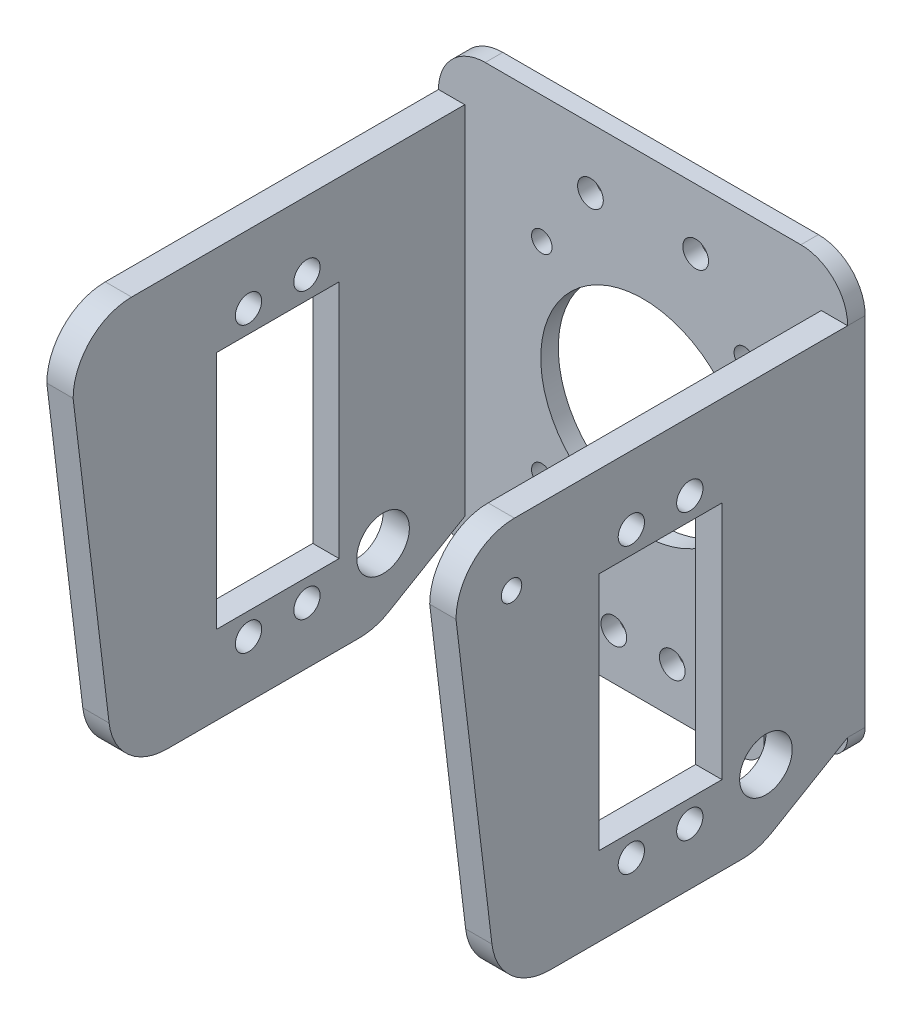
SolidWorks part; units mm, degrees
ref_plane "前视基准面" through (0, 0, 0) normal (0, 0, 1) x (1, 0, 0)
ref_plane "上视基准面" through (0, 0, 0) normal (0, 1, 0) x (1, 0, 0)
ref_plane "右视基准面" through (0, 0, 0) normal (1, 0, 0) x (0, 0, -1)
sketch "草图2" plane through (0, 0, 0) normal (0, 0, 1) x (1, 0, 0)
  line L0 (-31, -34) -> (-20.7251, -34)
  line L1 (-16.7251, -42) -> (16.7251, -42)
  line L2 (-35, -30) -> (-35, 31)
  line L3 (-27, 39) -> (27, 39)
  line L4 (35, -30) -> (35, 31)
  line L5 (-37.7907, -42.1097) -> (35, 39) construction
  line L6 (-35, 39) -> (30.3247, -33.7903) construction
  line L7 (-20.7251, -34) -> (-20.7251, -38)
  line L8 (0, 44.0576) -> (0, -51.8326) construction
  line L9 (20.7251, -34) -> (20.7251, -38)
  line L10 (31, -34) -> (20.7251, -34)
  line L16 (-17.3241, -17.3241) -> (17.3241, -17.3241) construction
  line L17 (-17.3241, -17.3241) -> (-17.3241, 17.3241) construction
  line L18 (-17.3241, 17.3241) -> (17.3241, 17.3241) construction
  line L19 (17.3241, -17.3241) -> (17.3241, 17.3241) construction
  line L20 (-17.3241, -17.3241) -> (17.3241, 17.3241) construction
  line L21 (-17.3241, 17.3241) -> (17.3241, -17.3241) construction
  arc A1 (-27, 39) -> (-35, 31) centre (-27, 31) ccw
  arc A2 (35, 31) -> (27, 39) centre (27, 31) ccw
  arc A3 (-31, -34) -> (-35, -30) centre (-31, -30) cw
  arc A4 (-16.7251, -42) -> (-20.7251, -38) centre (-16.7251, -38) cw
  arc A5 (20.7251, -38) -> (16.7251, -42) centre (16.7251, -38) cw
  arc A6 (35, -30) -> (31, -34) centre (31, -30) cw
  circle A19 centre (0, 0) radius 17.5
  circle A21 centre (-17.3241, 17.3241) radius 1.75
  circle A22 centre (17.3241, 17.3241) radius 1.75
  circle A23 centre (17.3241, -17.3241) radius 1.75
  circle A24 centre (-17.3241, -17.3241) radius 1.75
  point P0 (0, 0)
  point P24 (-35, -34)
  point P27 (-20.7251, -42)
  point P30 (20.7251, -42)
  point P33 (35, -34)
  point P45 (0, 0)
  point P49 (0, 0)
  point P50 (0, 0)
  dimension "D3" = 35
  dimension "D4" = 8
  dimension "D5" = 8
  dimension "D6" = 4
  dimension "D7" = 4
  dimension "D8" = 4
  dimension "D9" = 4
  dimension "D10" = 90
  dimension "D12" = 3.5
  dimension "D2" = 81
  dimension "D11" = 24.5
  dimension "D13" = 35
  dimension "D14" = 39
  dimension "D15" = 73
  dimension "D16" = 4
extrude "凸台-拉伸2" add sketch "草图2" along normal blind 3
sketch "草图4" plane through (0, 0, 3) normal (0, 0, 1) x (1, 0, 0)
  line L0 (35, -30) -> (35, 31) construction
  line L1 (30.5, -39) -> (35, -39)
  line L2 (30.5, -39) -> (30.5, 31)
  line L3 (30.5, 31) -> (35, 31)
  line L4 (35, -39) -> (35, 31)
  dimension "D1" = 4.5
  dimension "D2" = 70
extrude "凸台-拉伸3" add sketch "草图4" along normal blind 67 contours L2 L1 L4 L3
sketch "草图5" plane through (35, 0, 0) normal (1, 0, 0) x (0, 0, -1)
  line L2 (-3, -30) -> (0, -30) construction
  line L3 (-3, -39) -> (-3, -30) construction
  line L4 (-70, -39) -> (-3, -39) construction
  line L5 (-70, 31) -> (-3, 31) construction
  line L8 (-3, -30) -> (0, -30)
  line L9 (-3, -39) -> (-3, -30)
  line L10 (-53.9224, -39) -> (-21.0514, -39)
  line L11 (-60, 31) -> (-3, 31)
  line L12 (-3, 31) -> (-3, -30)
  line L13 (-70, 21) -> (-63.8511, -30.1926)
  line L15 (-28.4612, -39) -> (-53.9224, -39)
  line L17 (-15.9894, -37.6242) -> (-3, -30)
  line L19 (-21.0514, -39) -> (-3, -39)
  line L20 (-3, -30) -> (-3, -39)
  line L21 (-70, 21) -> (-70, 31)
  line L22 (-60, 31) -> (-70, 31)
  line L26 (0, -30) -> (0, 31)
  line L27 (0, 31) -> (-3, 31)
  line L28 (-3, 31) -> (-70, 31)
  line L29 (-70, 31) -> (-70, -39)
  line L30 (-70, -39) -> (-3, -39)
  line L31 (-3, -39) -> (-3, -30)
  line L32 (-3, -30) -> (0, -30)
  line L33 (0, -30) -> (0, 31)
  line L34 (0, 31) -> (-3, 31)
  line L35 (-3, 31) -> (-70, 31)
  line L36 (-70, 31) -> (-70, -39)
  line L37 (-70, -39) -> (-3, -39)
  line L38 (-3, -39) -> (-3, -30)
  line L39 (-3, -30) -> (0, -30)
  arc A0 (-70, 21) -> (-60, 31) centre (-60, 21) cw
  arc A1 (-53.9224, -39) -> (-63.8511, -30.1926) centre (-53.9224, -29) cw
  arc A2 (-15.9894, -37.6242) -> (-21.0514, -39) centre (-21.0514, -29) cw
  point P17 (-21.0514, -39)
  point P18 (-3, -30)
  line M12 (-3, 31) -> (-70, 31)
  line M13 (-70, 31) -> (-70, -39)
  line M14 (-70, -39) -> (-3, -39)
  line M15 (-3, -39) -> (-3, -30)
  dimension "D1" = 10
  dimension "D2" = 10
  dimension "D3" = 10
  dimension "D4" = 0
extrude "切除-拉伸4" cut sketch "草图5" against normal through all contours A0 M13 M12 | A1 L13 M14 M13 | L17 A2 M14 M15
mirror "镜向2" about plane through (0, 0, 0) normal (1, 0, 0) of "切除-拉伸4", "凸台-拉伸3"
sketch "草图6" plane through (35, 0, 0) normal (1, 0, 0) x (0, 0, -1)
  line L0 (0, 38.5) -> (0, -38.5) construction
  line L5 (-45.5, -32) -> (-24.5, -32)
  line L6 (-45.5, -32) -> (-45.5, 22)
  line L7 (-45.5, 22) -> (-24.5, 22)
  line L8 (-35, 22) -> (-35, -32) construction
  line L9 (-45.5, -5) -> (-24.5, -5) construction
  line L10 (-24.5, -32) -> (-24.5, 22)
  line L11 (-45.5, -32) -> (-24.5, 22) construction
  line L12 (-45.5, 22) -> (-24.5, -32) construction
  line L13 (-53.9224, -39) -> (-21.0514, -39) construction
  line L15 (-45.5, -25.5) -> (-24.5, -25.5)
  line L16 (-45.5, -25.5) -> (-45.5, 15.5)
  line L17 (-45.5, 15.5) -> (-24.5, 15.5)
  line L18 (-24.5, -25.5) -> (-24.5, 15.5)
  line L19 (-45.5, -25.5) -> (-24.5, 15.5) construction
  line L20 (-45.5, 15.5) -> (-24.5, -25.5) construction
  circle A0 centre (-40, -29.315) radius 2.25
  circle A2 centre (-30, -29.315) radius 2.25
  circle A3 centre (-30, 19.315) radius 2.25
  circle A4 centre (-40, 19.315) radius 2.25
  point P0 (-35, -5)
  point P21 (-35, -5)
  dimension "D5" = 21
  dimension "D6" = 4.5
  dimension "D1" = 54
  dimension "D2" = 21
  dimension "D3" = 35
  dimension "D4" = 34
  dimension "D7" = 10
  dimension "D8" = 41
  dimension "D9" = 48.63
extrude "切除-拉伸6" cut sketch "草图6" against normal through all contours A0 | A2 | L17 L6 L15 L10 | A4 | A3
sketch "草图7" plane through (35, 0, 0) normal (1, 0, 0) x (0, 0, -1)
  line L0 (-60, 31) -> (-3, 31) construction
  circle A0 centre (-60.5, 20.5) radius 1.75
  dimension "D1" = 3.5
  dimension "D2" = 10.5
  dimension "D3" = 9.5
extrude "切除-拉伸7" cut sketch "草图7" against normal up to next
sketch "草图8" plane through (35, 0, 0) normal (1, 0, 0) x (0, 0, -1)
  line L0 (-53.9224, -39) -> (-21.0514, -39) construction
  circle A0 centre (-16.9793, -27) radius 4.5
  dimension "D1" = 9
  dimension "D2" = 12
extrude "切除-拉伸8" cut sketch "草图8" against normal through all contours A0
sketch "草图9" plane through (0, 0, 3) normal (0, 0, 1) x (1, 0, 0)
  line L0 (0, 17.8493) -> (0, 0) construction
  line L1 (9.75, 17.15) -> (-9.75, 17.15)
  line L2 (9.75, 17.15) -> (9.75, -36.85)
  line L3 (9.75, -36.85) -> (-9.75, -36.85)
  line L4 (-9.75, 17.15) -> (-9.75, -36.85)
  line L5 (9.75, 17.15) -> (-9.75, -36.85) construction
  line L6 (9.75, -36.85) -> (-9.75, 17.15) construction
  line L7 (0, 0) -> (0, -36.85) construction
  line L8 (9.75, -9.85) -> (0, -9.85) construction
  line L9 (0, -9.85) -> (-9.75, -9.85) construction
  line L12 (-14, 33.65) -> (-14, -34.85)
  line L14 (14, 33.65) -> (14, -46.35)
  line L15 (-14, -39.85) -> (14, -39.85)
  line L18 (0, 17.8493) -> (0, 35.8623) construction
  line L20 (0, -6.35) -> (14, -6.35) construction
  line L21 (-14, -34.85) -> (-14, 33.65)
  line L22 (-14, -34.85) -> (-14, -39.85)
  line L23 (14, -46.35) -> (14, 33.65)
  line L25 (14, -46.35) -> (14, -39.85)
  line L26 (-14, 33.65) -> (14, 33.65)
  circle A0 centre (0, 0) radius 1.5
  circle A1 centre (5, -34.165) radius 2.2
  circle A2 centre (-5, -34.165) radius 2.2
  circle A3 centre (-5, 14.465) radius 2.2
  circle A4 centre (5, 14.465) radius 2.2
  circle A5 centre (9, 28.65) radius 2.2
  circle A6 centre (-9, 28.65) radius 2.2
  point P0 (0, -9.85)
  point P21 (0, -6.35)
  dimension "D4" = 3
  dimension "D5" = 4.4
  dimension "D6" = 4.4
  dimension "D14" = 4.4
  dimension "D15" = 4.4
  dimension "D19" = 14
  dimension "D24" = 14
  dimension "D1" = 54
  dimension "D2" = 19.5
  dimension "D3" = 17.15
  dimension "D7" = 5
  dimension "D8" = 5
  dimension "D9" = 48.63
  dimension "D10" = 48.63
  dimension "D11" = 3
  dimension "D12" = 33.5
  dimension "D13" = 40
  dimension "D16" = 5
  dimension "D17" = 5
  dimension "D18" = 5
  dimension "D23" = 5
extrude "切除-拉伸9" cut sketch "草图9" against normal through all contours A5 | A6 | A1 | A2
